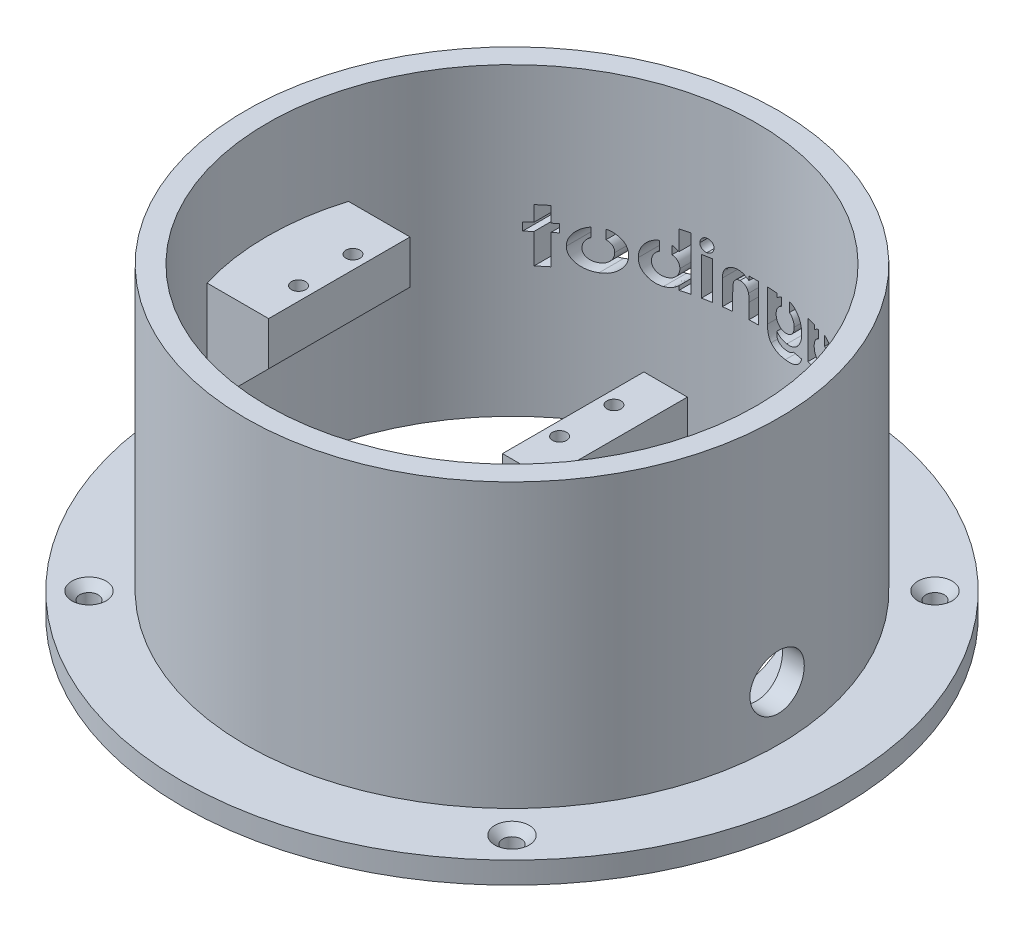
SolidWorks part; units mm, degrees
ref_plane "Front Plane" through (0, 0, 0) normal (0, 0, 1) x (1, 0, 0)
ref_plane "Top Plane" through (0, 0, 0) normal (0, 1, 0) x (1, 0, 0)
ref_plane "Right Plane" through (0, 0, 0) normal (1, 0, 0) x (0, 0, -1)
sketch "Sketch1" plane through (0, 0, 0) normal (0, 1, 0) x (1, 0, 0)
  circle A0 centre (0, 0) radius 60.625
  circle A1 centre (0, 0) radius 45
  dimension "D1" = 121.25
  dimension "D2" = 90
extrude "Boss-Extrude1" add sketch "Sketch1" along normal blind 4 contours A0
sketch "Sketch2" plane through (0, 4, 0) normal (0, 1, 0) x (1, 0, 0)
  circle A0 centre (0, 0) radius 45 construction
  circle A1 centre (0, 0) radius 45
  circle A2 centre (0, 0) radius 49
  dimension "D1" = 4
extrude "Boss-Extrude2" add sketch "Sketch2" along normal blind 52
ref_plane "Plane1" through (0, 36, 0) normal (0, 1, 0) x (1, 0, 0)
sketch "Sketch4" plane through (0, 0, 0) normal (0, 0, 1) x (1, 0, 0)
  line L0 (-60.625, 0) -> (60.625, 0) construction
  line L1 (11.25, 38) -> (19.25, 38)
  line L2 (11.25, 38) -> (11.25, 0)
  line L3 (11.25, 0) -> (19.25, 0)
  line L4 (19.25, 38) -> (19.25, 0)
  line L5 (49, 56) -> (-49, 56) construction
  line L6 (-45, 56) -> (-45, 4)
  line L7 (-31.75, 38) -> (-46.75, 38)
  line L8 (-31.75, 38) -> (-31.75, 30)
  line L9 (-31.75, 30) -> (-46.75, 30)
  line L10 (-46.75, 38) -> (-46.75, 30)
  line L11 (60.625, 4) -> (-60.625, 4) construction
  line L12 (-31.75, 30) -> (-45, 16.75)
  dimension "D1" = 11.25
  dimension "D2" = 8
  dimension "D3" = 18
  dimension "D4" = 43
  dimension "D5" = 15
  dimension "D6" = 8
  dimension "D7" = 45
  dimension "D8" = 18
extrude "Boss-Extrude4" add sketch "Sketch4" along normal mid plane 26 contours L9 L8 L7 L6 | L12 L9 L6 | L1 L4 L3 L2
sketch "Sketch5" plane through (0, 0, 0) normal (0, -1, 0) x (1, 0, 0)
  line L0 (11.25, 13) -> (29.0674, 34.3524)
  line L1 (11.25, -13) -> (29.0674, -34.3524)
  line L2 (11.25, 13) -> (11.25, -13)
  circle A0 centre (0, 0) radius 45 construction
  arc A1 (29.0674, -34.3524) -> (29.0674, 34.3524) centre (0, 0) ccw
extrude "Boss-Extrude5" add sketch "Sketch5" against normal up to surface (4 mm away) contours L0 A1 L1 L2 up to face at (0, 4, 60.625)
sketch "Sketch7" plane through (0, 38, 0) normal (0, 1, 0) x (1, 0, 0)
  line L0 (-31.75, -13) -> (-31.75, 13) construction
  circle A0 centre (-34.25, 5) radius 1.3
  circle A1 centre (-34.25, -5) radius 1.3
  circle A2 centre (13.75, 5) radius 1.3
  circle A3 centre (13.75, -5) radius 1.3
  dimension "D1" = 2.6
  dimension "D2" = 2.6
  dimension "D3" = 10
  dimension "D4" = 5
  dimension "D5" = 2.5
  dimension "D7" = 48
  dimension "D6" = 2
extrude "Cut-Extrude4" cut sketch "Sketch7" against normal blind 7.2
sketch "Sketch9" plane through (11.25, 0, 0) normal (-1, 0, 0) x (0, 0, 1)
  line L0 (13, 0) -> (-13, 0) construction
  line L1 (-5, 29) -> (5, 29)
  line L2 (-5, 29) -> (-5, 0)
  line L3 (-5, 0) -> (5, 0)
  line L4 (5, 29) -> (5, 0)
  line L5 (-5, 29) -> (5, 0) construction
  line L6 (-5, 0) -> (5, 29) construction
  line L7 (0, 0) -> (0, 29) construction
  line L8 (13, 38) -> (-13, 38) construction
  line L10 (5, 5) -> (-5, 5)
  point P0 (0, 14.5)
  dimension "D1" = 10
  dimension "D2" = 9
  dimension "D3" = 5
extrude "Cut-Extrude7" cut sketch "Sketch9" against normal up to surface (8 mm away) contours L10 L4 L1 L2 up to face at (19.25, 21, 0)
ref_plane "Plane2" through (49, 0, 0) normal (1, 0, 0) x (0, 0, -1)
sketch "Sketch11" plane through (49, 0, 0) normal (1, 0, 0) x (0, 0, -1)
  circle A0 centre (0, 14) radius 5
  dimension "D1" = 10
  dimension "D2" = 14
extrude "Cut-Extrude8" cut sketch "Sketch11" against normal up to next
sketch "Sketch12" plane through (0, 4, 0) normal (0, 1, 0) x (1, 0, 0)
  line L5 (27.25, 19.6878) -> (27.25, -19.6878)
  line L6 (27.25, 19.6878) -> (27.25, -19.6878)
  line L9 (24.25, 16.0926) -> (24.25, -16.0926)
  line L10 (19.25, -13) -> (19.25, 13) construction
  line L18 (27.25, -19.6878) -> (29.4795, -22.3597)
  line L19 (29.4795, 22.3597) -> (27.25, 19.6878)
  line L21 (24.25, -16.0926) -> (29.4795, -22.3597)
  line L22 (29.4795, 22.3597) -> (24.25, 16.0926)
  arc A2 (29.4795, -22.3597) -> (29.4795, 22.3597) centre (0, 0) ccw
  arc A3 (29.4795, -22.3597) -> (29.4795, 22.3597) centre (0, 0) ccw
  dimension "D2" = 5
  dimension "D1" = 8
extrude "Cut-Extrude9" cut sketch "Sketch12" against normal through all contours L21 A3 L22 L6 | L6 L22 L9 L21
sketch "Sketch14" plane through (0, 4, 0) normal (0, 1, 0) x (1, 0, 0)
  line L0 (0, 0) -> (-38.8909, 38.8909) construction
  line L1 (11.25, 13) -> (19.25, 13) construction
  circle A0 centre (-38.8909, 38.8909) radius 1.5
  circle A1 centre (38.8909, 38.8909) radius 1.5
  circle A2 centre (38.8909, -38.8909) radius 1.5
  circle A3 centre (-38.8909, -38.8909) radius 1.5
  point P15 (0, 0)
  dimension "D1" = 3
  dimension "D2" = 55
  dimension "D3" = 135
  dimension "D4" = 4
hole_wizard "CSK for M3 Countersunk Flat Head Screw1" positions "Sketch15" profile "Sketch17" countersink size "M3" standard "DIN" end condition up to next
sketch "Sketch15" plane through (0, 4, 0) normal (0, 1, 0) x (1, 0, 0)
  point P0 (-38.8909, 38.8909)
  point P3 (-38.8909, -38.8909)
  point P6 (38.8909, -38.8909)
  point P9 (38.8909, 38.8909)
sketch "Sketch17" plane through (-38.8909, 4, -38.8909) normal (1, 0, 0) x (0, 0, 1)
  line L0 (0, 0) -> (0, 4)
  line L1 (0, 4) -> (1.7, 4)
  line L2 (1.7, 4) -> (1.7, 1.45)
  line L3 (1.7, 1.45) -> (3.15, 0)
  line L5 (3.15, 0) -> (0, 0)
  line L6 (-1.7, 1.45) -> (-3.15, 0) construction
  line L11 (0, -6.35) -> (0, 107.95) construction
  dimension "Thru Hole Dia." = 3.4
  dimension "Thru Hole Depth" = 4
  dimension "Near C'Sink Dia." = 6.3
  dimension "Near C'Sink Angle" = 90
sketch "Sketch18" plane through (0, 0, -13) normal (0, 0, -1) x (-1, 0, 0)
  line L1 (28.0255, 33.7692) -> (29.7351, 33.7692)
  line L2 (29.7351, 33.7692) -> (29.7351, 30.9606)
  line L3 (29.7351, 30.9606) -> (30.8341, 30.9606)
  line L4 (30.8341, 30.9606) -> (30.8341, 29.4952)
  line L5 (30.8341, 29.4952) -> (29.7351, 29.4952)
  line L6 (29.7351, 29.4952) -> (29.7351, 24)
  line L7 (29.7351, 24) -> (28.0255, 24)
  line L8 (28.0255, 24) -> (28.0255, 29.4952)
  line L9 (28.0255, 29.4952) -> (27.1707, 29.4952)
  line L10 (27.1707, 29.4952) -> (27.1707, 30.9606)
  line L11 (27.1707, 30.9606) -> (28.0255, 30.9606)
  line L12 (28.0255, 30.9606) -> (28.0255, 33.7692)
  line L13 (12.5168, 33.7692) -> (12.5168, 30.1497)
  line L14 (12.5168, 24.7594) -> (12.5168, 24)
  line L15 (12.5168, 24) -> (10.8072, 24)
  line L16 (10.8072, 24) -> (10.8072, 33.7692)
  line L17 (10.8072, 33.7692) -> (12.5168, 33.7692)
  line L18 (7.5101, 30.9606) -> (9.2197, 30.9606)
  line L19 (9.2197, 30.9606) -> (9.2197, 24)
  line L20 (9.2197, 24) -> (7.5101, 24)
  line L21 (7.5101, 24) -> (7.5101, 30.9606)
  line L22 (-0.3053, 30.9606) -> (1.4043, 30.9606)
  line L23 (1.4043, 30.9606) -> (1.4043, 30.2241)
  line L24 (5.9226, 28.5641) -> (5.9226, 24)
  line L25 (5.9226, 24) -> (4.213, 24)
  line L26 (4.213, 24) -> (4.213, 27.0224)
  line L27 (1.4043, 26.7705) -> (1.4043, 24)
  line L28 (1.4043, 24) -> (-0.3053, 24)
  line L29 (-0.3053, 24) -> (-0.3053, 30.9606)
  line L30 (-3.8466, 30.9606) -> (-2.0149, 30.9606)
  line L31 (-2.0149, 30.9606) -> (-2.0149, 25.0227)
  line L32 (-9.2273, 23.5115) -> (-7.3269, 23.5115)
  line L33 (-3.8466, 30.1859) -> (-3.8466, 30.9606)
  line L34 (-12.3947, 30.9606) -> (-10.6851, 30.9606)
  line L35 (-10.6851, 30.9606) -> (-10.6851, 24)
  line L36 (-10.6851, 24) -> (-12.3947, 24)
  line L37 (-12.3947, 24) -> (-12.3947, 24.7594)
  line L38 (-12.3947, 30.1764) -> (-12.3947, 30.9606)
  line L39 (-30.1014, 30.9606) -> (-28.3918, 30.9606)
  line L40 (-28.3918, 30.9606) -> (-28.3918, 30.1287)
  line L41 (-19.3553, 28.0489) -> (-19.3553, 24)
  line L42 (-19.3553, 24) -> (-21.0649, 24)
  line L43 (-21.0649, 24) -> (-21.0649, 27.4956)
  line L44 (-23.8736, 27.1082) -> (-23.8736, 24)
  line L45 (-23.8736, 24) -> (-25.5832, 24)
  line L46 (-25.5832, 24) -> (-25.5832, 27.3372)
  line L47 (-28.3918, 27.0643) -> (-28.3918, 24)
  line L48 (-28.3918, 24) -> (-30.1014, 24)
  line L49 (-30.1014, 24) -> (-30.1014, 30.9606)
  line L51 (-15.1048, 31.4629) -> (-13.3948, 31.4629)
  line L52 (-15.1048, 31.4629) -> (-15.1048, 28.9712)
  line L53 (-15.1048, 28.9712) -> (-13.3948, 28.9712)
  line L54 (-13.3948, 31.4629) -> (-13.3948, 28.9712)
  line L55 (-6.4773, 31.5143) -> (-4.7673, 31.5143)
  line L56 (-6.4773, 31.5143) -> (-6.4773, 29.0876)
  line L57 (-6.4773, 29.0876) -> (-4.7673, 29.0876)
  line L58 (-4.7673, 31.5143) -> (-4.7673, 29.0876)
  line L59 (13.5081, 31.593) -> (15.2181, 31.593)
  line L60 (13.5081, 31.593) -> (13.5081, 28.9616)
  line L61 (13.5081, 28.9616) -> (15.2181, 28.9616)
  line L62 (15.2181, 31.593) -> (15.2181, 28.9616)
  line L63 (21.9818, 31.4887) -> (23.6918, 31.4887)
  line L64 (21.9818, 31.4887) -> (21.9818, 28.7761)
  line L65 (21.9818, 28.7761) -> (23.6918, 28.7761)
  line L66 (23.6918, 31.4887) -> (23.6918, 28.7761)
  spline S0 degree 3 poles (22.7936, 31.0827) (22.9536, 31.0827) (23.1931, 31.0681) (23.5072, 31.016) (23.7386, 30.9659) (23.965, 30.8957) (24.1877, 30.8115) (24.4086, 30.7149) (24.6222, 30.5998) (24.83, 30.4751) (25.0271, 30.3374) (25.2118, 30.188) (25.3874, 30.0303) (25.5458, 29.8573) (25.6972, 29.6776) (25.8334, 29.4845) (25.9594, 29.2828) (26.0716, 29.0738) (26.169, 28.8587) (26.2536, 28.6407) (26.3198, 28.417) (26.3746, 28.1906) (26.4213, 27.88) (26.4389, 27.6443) (26.438, 27.486) knots 0 0 0 0 0.084364 0.126142 0.167706 0.209066 0.250973 0.293148 0.336041 0.378761 0.420893 0.462622 0.503914 0.545188 0.586138 0.627722 0.669585 0.711432 0.752691 0.793971 0.834592 0.875577 0.91664 1 1 1 1
  spline S1 degree 3 poles (26.438, 27.486) (26.4378, 27.3266) (26.4236, 27.0883) (26.3713, 26.7763) (26.321, 26.5461) (26.2511, 26.3218) (26.1694, 26.1) (26.0691, 25.8836) (25.9582, 25.6704) (25.8314, 25.4666) (25.6953, 25.2716) (25.5446, 25.0905) (25.3874, 24.9177) (25.2164, 24.759) (25.0341, 24.6119) (24.8423, 24.4746) (24.6396, 24.3502) (24.4285, 24.2409) (24.2126, 24.1424) (23.9906, 24.0604) (23.763, 23.9934) (23.5297, 23.9417) (23.2093, 23.8941) (22.9652, 23.8771) (22.8012, 23.8779) knots 0 0 0 0 0.083839 0.125192 0.166335 0.207602 0.24867 0.290582 0.332926 0.374978 0.416741 0.457857 0.498809 0.539516 0.58042 0.62191 0.663502 0.705394 0.746864 0.788245 0.829736 0.871532 0.913825 1 1 1 1
  spline S2 degree 3 poles (22.8012, 23.8779) (22.5631, 23.8803) (22.2083, 23.9072) (21.7532, 24.019) (21.429, 24.1339) (21.1177, 24.2814) (20.822, 24.4638) (20.5389, 24.6777) (20.2733, 24.9212) (20.03, 25.1884) (19.8174, 25.4736) (19.6369, 25.7726) (19.4887, 26.0857) (19.3743, 26.4132) (19.2623, 26.874) (19.2355, 27.2332) (19.2332, 27.4746) knots 0 0 0 0 0.126884 0.188201 0.248894 0.309599 0.371125 0.433466 0.498143 0.562593 0.625474 0.687114 0.748125 0.809457 0.871431 1 1 1 1
  spline S3 degree 3 poles (19.2332, 27.4746) (19.2336, 27.7324) (19.2684, 28.1141) (19.3922, 28.6033) (19.5227, 28.9481) (19.6897, 29.2762) (19.9647, 29.6971) (20.2255, 29.9763) (20.4143, 30.1497) knots 0 0 0 0 0.256474 0.379237 0.500978 0.622367 0.744855 1 1 1 1
  spline S4 degree 3 poles (20.4143, 30.1497) (20.5802, 30.3024) (20.8481, 30.5037) (21.2311, 30.7219) (21.5244, 30.8552) (21.8286, 30.9555) (22.2495, 31.0542) (22.575, 31.0818) (22.7936, 31.0827) knots 0 0 0 0 0.258464 0.38258 0.504991 0.627227 0.749297 1 1 1 1
  spline S5 degree 3 poles (22.8318, 29.4952) (22.7019, 29.4917) (22.5077, 29.4823) (22.2621, 29.4178) (22.0874, 29.3572) (21.9227, 29.2762) (21.7633, 29.1814) (21.6176, 29.0627) (21.4785, 28.9326) (21.3522, 28.7881) (21.2446, 28.6306) (21.1485, 28.4663) (21.0755, 28.289) (21.0153, 28.1036) (20.9595, 27.8373) (20.9404, 27.6306) (20.9428, 27.4898) knots 0 0 0 0 0.126803 0.187423 0.246518 0.306285 0.365703 0.426477 0.488622 0.550895 0.612679 0.673914 0.735734 0.798735 0.86329 1 1 1 1
  spline S6 degree 3 poles (20.9428, 27.4898) (20.9422, 27.3456) (20.9565, 27.1333) (21.0136, 26.8609) (21.0729, 26.672) (21.1476, 26.4928) (21.2392, 26.3242) (21.3487, 26.1674) (21.4728, 26.0226) (21.6088, 25.891) (21.7577, 25.7782) (21.9134, 25.6801) (22.0795, 25.6014) (22.2535, 25.5406) (22.5012, 25.4797) (22.6954, 25.468) (22.826, 25.4654) knots 0 0 0 0 0.139456 0.204809 0.268587 0.330587 0.392213 0.45361 0.515092 0.576402 0.636039 0.695407 0.753981 0.813285 0.873377 1 1 1 1
  spline S7 degree 3 poles (22.826, 25.4654) (22.9571, 25.4658) (23.1512, 25.4829) (23.3999, 25.5421) (23.5754, 25.6033) (23.7416, 25.6838) (23.899, 25.7823) (24.0491, 25.8968) (24.1868, 26.0308) (24.3144, 26.1761) (24.4262, 26.3337) (24.5196, 26.5022) (24.5963, 26.6806) (24.6557, 26.8685) (24.7119, 27.1379) (24.7308, 27.3472) (24.7284, 27.4898) knots 0 0 0 0 0.126397 0.186939 0.246099 0.305348 0.364572 0.424924 0.486952 0.54955 0.611149 0.672922 0.73501 0.798049 0.862643 1 1 1 1
  spline S8 degree 3 poles (24.7284, 27.4898) (24.7289, 27.6322) (24.7144, 27.8419) (24.6579, 28.1106) (24.5978, 28.2968) (24.5236, 28.4736) (24.4319, 28.6402) (24.3219, 28.7958) (24.1971, 28.9395) (24.0592, 29.0692) (23.9128, 29.1849) (23.7547, 29.2805) (23.5879, 29.3593) (23.4118, 29.42) (23.161, 29.4811) (22.9643, 29.4923) (22.8318, 29.4952) knots 0 0 0 0 0.13784 0.202698 0.265406 0.326938 0.388125 0.449117 0.511101 0.572086 0.632197 0.691339 0.750564 0.810546 0.871335 1 1 1 1
  spline S9 degree 3 poles (12.5168, 30.1497) (12.6689, 30.2999) (12.913, 30.5045) (13.2701, 30.721) (13.5425, 30.8554) (13.8263, 30.9547) (14.2179, 31.0586) (14.5242, 31.079) (14.7283, 31.0827) knots 0 0 0 0 0.260396 0.385476 0.507708 0.62942 0.750914 1 1 1 1
  spline S10 degree 3 poles (14.7283, 31.0827) (14.9489, 31.0835) (15.2774, 31.0537) (15.6975, 30.9454) (15.9965, 30.8341) (16.2816, 30.6893) (16.5559, 30.5161) (16.8147, 30.3071) (17.0582, 30.0704) (17.2834, 29.811) (17.4794, 29.5289) (17.6425, 29.228) (17.7809, 28.9116) (17.8817, 28.5747) (17.9877, 28.0953) (18.0097, 27.72) (18.012, 27.4669) knots 0 0 0 0 0.12138 0.180256 0.238142 0.296489 0.355776 0.416247 0.479076 0.54232 0.604902 0.667516 0.730346 0.794405 0.860608 1 1 1 1
  spline S11 degree 3 poles (18.012, 27.4669) (18.0112, 27.2212) (17.9853, 26.8569) (17.8789, 26.39) (17.7693, 26.061) (17.6298, 25.7471) (17.4595, 25.4483) (17.2574, 25.1658) (17.0264, 24.9033) (16.774, 24.6656) (16.511, 24.4523) (16.2322, 24.2776) (15.9446, 24.1299) (15.6435, 24.0172) (15.2231, 23.91) (14.8966, 23.875) (14.6767, 23.8779) knots 0 0 0 0 0.135343 0.199959 0.263049 0.325881 0.388744 0.451973 0.516706 0.580831 0.6426 0.702706 0.761562 0.820266 0.879182 1 1 1 1
  spline S12 degree 3 poles (14.6767, 23.8779) (14.4813, 23.879) (14.1903, 23.9014) (13.8164, 23.9898) (13.5471, 24.0796) (13.2849, 24.2024) (12.9279, 24.4129) (12.6786, 24.6134) (12.5168, 24.7594) knots 0 0 0 0 0.245253 0.364043 0.481077 0.600625 0.726476 1 1 1 1
  spline S13 degree 3 poles (14.3581, 29.4952) (14.2224, 29.4925) (14.0206, 29.4811) (13.7637, 29.4198) (13.5821, 29.3613) (13.4104, 29.2824) (13.2472, 29.1868) (13.0939, 29.0727) (12.9496, 28.9448) (12.82, 28.8008) (12.7049, 28.647) (12.6094, 28.4813) (12.5298, 28.3059) (12.4697, 28.1188) (12.409, 27.8506) (12.3972, 27.6408) (12.3947, 27.4994) knots 0 0 0 0 0.129944 0.191681 0.251804 0.311878 0.37178 0.43216 0.494106 0.5556 0.61683 0.677256 0.737884 0.800505 0.864611 1 1 1 1
  spline S14 degree 3 poles (12.3947, 27.4994) (12.3973, 27.3547) (12.409, 27.1406) (12.4693, 26.8672) (12.5306, 26.6767) (12.6089, 26.497) (12.7043, 26.3272) (12.8207, 26.1712) (12.9489, 26.0235) (13.094, 25.8938) (13.2466, 25.7775) (13.4104, 25.6817) (13.5829, 25.6041) (13.7629, 25.5396) (14.0209, 25.4803) (14.2222, 25.4676) (14.3581, 25.4654) knots 0 0 0 0 0.137034 0.201676 0.264245 0.325918 0.386785 0.447889 0.509667 0.571399 0.631536 0.690841 0.750317 0.810229 0.871351 1 1 1 1
  spline S15 degree 3 poles (14.3581, 25.4654) (14.4904, 25.4663) (14.6858, 25.4825) (14.9372, 25.5423) (15.1143, 25.6051) (15.2837, 25.6869) (15.4466, 25.7826) (15.5976, 25.9021) (15.7426, 26.0336) (15.8723, 26.1818) (15.9886, 26.3392) (16.0864, 26.5074) (16.164, 26.6867) (16.2281, 26.8738) (16.2876, 27.1426) (16.2999, 27.3521) (16.3024, 27.4936) knots 0 0 0 0 0.1264 0.186368 0.246314 0.305548 0.365765 0.426397 0.489164 0.552425 0.614149 0.675935 0.737677 0.800494 0.864605 1 1 1 1
  spline S16 degree 3 poles (16.3024, 27.4936) (16.2994, 27.6337) (16.2886, 27.8419) (16.2268, 28.1069) (16.1694, 28.2934) (16.0892, 28.4684) (15.9943, 28.634) (15.8827, 28.7908) (15.7531, 28.9344) (15.6111, 29.0651) (15.4595, 29.1807) (15.2988, 29.2792) (15.127, 29.3568) (14.9481, 29.4206) (14.6922, 29.4804) (14.4927, 29.4929) (14.3581, 29.4952) knots 0 0 0 0 0.134802 0.198611 0.260756 0.321667 0.382903 0.4437 0.505935 0.568128 0.628667 0.688638 0.748437 0.809234 0.870665 1 1 1 1
  spline S17 degree 3 poles (8.3611, 33.8913) (8.5057, 33.8937) (8.7226, 33.8489) (8.977, 33.7027) (9.1452, 33.5539) (9.285, 33.3759) (9.4295, 33.1075) (9.4611, 32.8768) (9.4639, 32.7255) knots 0 0 0 0 0.242963 0.363855 0.490606 0.61874 0.7433 1 1 1 1
  spline S18 degree 3 poles (9.4639, 32.7255) (9.4628, 32.5754) (9.4267, 32.3489) (9.2879, 32.0806) (9.147, 31.9053) (8.9806, 31.7588) (8.732, 31.6103) (8.5162, 31.5712) (8.3744, 31.5712) knots 0 0 0 0 0.256469 0.381955 0.510704 0.637377 0.757775 1 1 1 1
  spline S19 degree 3 poles (8.3744, 31.5712) (8.2284, 31.5686) (8.0103, 31.614) (7.7524, 31.7591) (7.5849, 31.9109) (7.4436, 32.0902) (7.3049, 32.3653) (7.2655, 32.5959) (7.2659, 32.7503) knots 0 0 0 0 0.242759 0.363443 0.489711 0.617482 0.74228 1 1 1 1
  spline S20 degree 3 poles (7.2659, 32.7503) (7.2683, 32.8988) (7.3018, 33.124) (7.4428, 33.3874) (7.5816, 33.5622) (7.7483, 33.7082) (8.0025, 33.8499) (8.2174, 33.8925) (8.3611, 33.8913) knots 0 0 0 0 0.255027 0.378937 0.506523 0.634371 0.754976 1 1 1 1
  spline S21 degree 3 poles (1.4043, 30.2241) (1.5881, 30.3723) (1.8638, 30.5692) (2.2391, 30.781) (2.4966, 30.8962) (2.749, 30.9789) (3.0835, 31.0586) (3.3399, 31.0837) (3.5108, 31.0827) knots 0 0 0 0 0.304989 0.436681 0.556242 0.668759 0.779379 1 1 1 1
  spline S22 degree 3 poles (3.5108, 31.0827) (3.6804, 31.0808) (3.9334, 31.0645) (4.2568, 30.9851) (4.4874, 30.9076) (4.7072, 30.8051) (4.9922, 30.6415) (5.182, 30.4798) (5.3025, 30.3653) knots 0 0 0 0 0.257369 0.381171 0.503299 0.625248 0.747811 1 1 1 1
  spline S23 degree 3 poles (5.3025, 30.3653) (5.4059, 30.2627) (5.5432, 30.0886) (5.6853, 29.8262) (5.7737, 29.6095) (5.8389, 29.3729) (5.908, 29.0248) (5.9215, 28.7507) (5.9226, 28.5641) knots 0 0 0 0 0.22321 0.337546 0.456528 0.581244 0.713405 1 1 1 1
  spline S24 degree 3 poles (4.213, 27.0224) (4.2125, 27.2112) (4.2108, 27.4817) (4.1962, 27.8244) (4.1868, 28.0428) (4.1682, 28.2348) (4.1514, 28.4014) (4.1257, 28.5411) (4.0922, 28.6915) (4.0338, 28.8525) (3.943, 29.0221) (3.8279, 29.1662) (3.6932, 29.2858) (3.5389, 29.3803) (3.303, 29.4721) (3.1097, 29.4957) (2.9785, 29.4952) knots 0 0 0 0 0.179518 0.256937 0.32593 0.387213 0.440139 0.484952 0.522188 0.586422 0.647004 0.704202 0.760716 0.817414 0.875213 1 1 1 1
  spline S25 degree 3 poles (2.9785, 29.4952) (2.8055, 29.4934) (2.5449, 29.4553) (2.234, 29.3024) (2.0255, 29.1462) (1.8416, 28.9531) (1.6327, 28.637) (1.531, 28.3636) (1.4845, 28.171) knots 0 0 0 0 0.240658 0.35739 0.477137 0.600009 0.725225 1 1 1 1
  spline S26 degree 3 poles (1.4845, 28.171) (1.4665, 28.1021) (1.4533, 27.9851) (1.4322, 27.8146) (1.4255, 27.6513) (1.4141, 27.4645) (1.4081, 27.168) (1.4044, 26.934) (1.4043, 26.7705) knots 0 0 0 0 0.151476 0.251213 0.366854 0.500124 0.650932 1 1 1 1
  spline S27 degree 3 poles (-2.0149, 25.0227) (-2.0161, 24.7489) (-2.0329, 24.3502) (-2.1079, 23.8416) (-2.1856, 23.5018) (-2.2863, 23.192) (-2.4455, 22.8255) (-2.6034, 22.5793) (-2.7266, 22.4354) knots 0 0 0 0 0.300234 0.436257 0.562885 0.681681 0.792784 1 1 1 1
  spline S28 degree 3 poles (-2.7266, 22.4354) (-2.8834, 22.2492) (-3.1574, 22.0013) (-3.5792, 21.7441) (-3.9268, 21.5849) (-4.3051, 21.4638) (-4.8649, 21.3434) (-5.3059, 21.3128) (-5.6078, 21.3135) knots 0 0 0 0 0.228421 0.343997 0.462956 0.586703 0.716303 1 1 1 1
  spline S29 degree 3 poles (-5.6078, 21.3135) (-5.9233, 21.3133) (-6.3802, 21.3376) (-6.9551, 21.4475) (-7.33, 21.5582) (-7.6699, 21.7012) (-7.9812, 21.8726) (-8.2633, 22.0776) (-8.5206, 22.3079) (-8.7467, 22.5689) (-9.0083, 22.9588) (-9.1528, 23.2846) (-9.2273, 23.5115) knots 0 0 0 0 0.207411 0.299345 0.383942 0.46371 0.541137 0.616855 0.692287 0.767513 0.843065 1 1 1 1
  spline S30 degree 3 poles (-7.3269, 23.5115) (-7.2424, 23.411) (-7.0944, 23.2762) (-6.8653, 23.1368) (-6.6744, 23.0501) (-6.4646, 22.9844) (-6.1522, 22.9154) (-5.9045, 22.902) (-5.7356, 22.901) knots 0 0 0 0 0.223655 0.337943 0.455777 0.579824 0.711809 1 1 1 1
  spline S31 degree 3 poles (-5.7356, 22.901) (-5.5252, 22.8993) (-5.2245, 22.9236) (-4.8512, 23.0143) (-4.621, 23.1109) (-4.4224, 23.227) (-4.2567, 23.3619) (-4.1198, 23.5105) (-4.0303, 23.6502) (-3.9771, 23.777) (-3.9409, 23.8865) (-3.9134, 24.0127) (-3.8884, 24.1533) (-3.8697, 24.31) (-3.8523, 24.5498) (-3.8442, 24.7376) (-3.8466, 24.8682) knots 0 0 0 0 0.197721 0.282266 0.359994 0.431569 0.49787 0.56009 0.620807 0.652682 0.689174 0.72906 0.773983 0.823375 0.87735 1 1 1 1
  spline S32 degree 3 poles (-3.8466, 24.8682) (-3.9891, 24.7215) (-4.2155, 24.5237) (-4.5479, 24.3175) (-4.7977, 24.1973) (-5.0596, 24.1094) (-5.435, 24.0229) (-5.7297, 24.001) (-5.9302, 24) knots 0 0 0 0 0.263928 0.385524 0.503705 0.620733 0.741155 1 1 1 1
  spline S33 degree 3 poles (-5.9302, 24) (-6.1529, 23.9985) (-6.4834, 24.0299) (-6.9074, 24.1357) (-7.2089, 24.2439) (-7.4948, 24.3877) (-7.7693, 24.5588) (-8.0273, 24.7661) (-8.2723, 24.9982) (-8.4938, 25.2561) (-8.6886, 25.5331) (-8.8529, 25.8273) (-8.9865, 26.1384) (-9.0929, 26.4651) (-9.1927, 26.932) (-9.2188, 27.2956) (-9.2197, 27.5413) knots 0 0 0 0 0.1237 0.183445 0.242476 0.301273 0.360988 0.421869 0.484864 0.548268 0.610431 0.67277 0.73514 0.798288 0.86338 1 1 1 1
  spline S34 degree 3 poles (-9.2197, 27.5413) (-9.2211, 27.8026) (-9.1909, 28.1873) (-9.0852, 28.6807) (-8.9753, 29.0233) (-8.8304, 29.3443) (-8.5973, 29.747) (-8.3769, 30.0193) (-8.2104, 30.1821) knots 0 0 0 0 0.269734 0.396745 0.520319 0.640547 0.759724 1 1 1 1
  spline S35 degree 3 poles (-8.2104, 30.1821) (-8.0629, 30.3284) (-7.8246, 30.5246) (-7.4774, 30.7358) (-7.2084, 30.8619) (-6.9288, 30.9621) (-6.5361, 31.0571) (-6.2309, 31.0833) (-6.0256, 31.0827) knots 0 0 0 0 0.256681 0.379784 0.501471 0.623319 0.746312 1 1 1 1
  spline S36 degree 3 poles (-6.0256, 31.0827) (-5.8329, 31.0809) (-5.544, 31.0597) (-5.1722, 30.9687) (-4.9013, 30.8759) (-4.6336, 30.7555) (-4.2695, 30.5388) (-4.0124, 30.3368) (-3.8466, 30.1859) knots 0 0 0 0 0.2398 0.357658 0.474596 0.595177 0.721609 1 1 1 1
  spline S37 degree 3 poles (-5.6173, 29.4952) (-5.7486, 29.4924) (-5.9441, 29.481) (-6.1927, 29.4198) (-6.3686, 29.3613) (-6.5347, 29.2825) (-6.6914, 29.1864) (-6.8405, 29.0749) (-6.9773, 28.9458) (-7.1041, 28.8063) (-7.2105, 28.6527) (-7.3054, 28.4939) (-7.3792, 28.3235) (-7.4401, 28.1459) (-7.4912, 27.8909) (-7.5138, 27.6945) (-7.5101, 27.5604) knots 0 0 0 0 0.130325 0.192491 0.253031 0.313597 0.374077 0.434784 0.49761 0.560052 0.621032 0.682272 0.742887 0.804621 0.867736 1 1 1 1
  spline S38 degree 3 poles (-7.5101, 27.5604) (-7.5126, 27.4216) (-7.4934, 27.218) (-7.4376, 26.9553) (-7.3761, 26.7729) (-7.2989, 26.5991) (-7.2063, 26.4341) (-7.0919, 26.2817) (-6.9648, 26.1386) (-6.8243, 26.0093) (-6.6731, 25.8968) (-6.5142, 25.7996) (-6.3442, 25.7239) (-6.1669, 25.6625) (-5.9146, 25.6021) (-5.7175, 25.5901) (-5.5849, 25.5875) knots 0 0 0 0 0.134675 0.197932 0.260448 0.321294 0.382443 0.443854 0.505984 0.568072 0.628986 0.688849 0.748568 0.809329 0.870916 1 1 1 1
  spline S39 degree 3 poles (-5.5849, 25.5875) (-5.4549, 25.585) (-5.2638, 25.604) (-5.0182, 25.6605) (-4.8459, 25.7195) (-4.6833, 25.7967) (-4.5283, 25.8887) (-4.3842, 26) (-4.2481, 26.1259) (-4.1254, 26.2659) (-4.017, 26.4176) (-3.928, 26.581) (-3.8521, 26.7535) (-3.796, 26.9376) (-3.7378, 27.2011) (-3.7243, 27.4074) (-3.7245, 27.5471) knots 0 0 0 0 0.128347 0.189068 0.248938 0.308024 0.366703 0.426834 0.487805 0.549753 0.610659 0.671749 0.733442 0.796702 0.861717 1 1 1 1
  spline S40 degree 3 poles (-3.7245, 27.5471) (-3.724, 27.6849) (-3.7381, 27.8886) (-3.7959, 28.149) (-3.8527, 28.3315) (-3.9269, 28.5039) (-4.02, 28.6647) (-4.1263, 28.8169) (-4.2516, 28.9552) (-4.3866, 29.0832) (-4.5355, 29.1914) (-4.6907, 29.2871) (-4.8576, 29.3629) (-5.034, 29.4225) (-5.2869, 29.4785) (-5.4835, 29.4978) (-5.6173, 29.4952) knots 0 0 0 0 0.135592 0.199609 0.261895 0.32322 0.383708 0.44425 0.505361 0.566852 0.626748 0.685936 0.745803 0.8065 0.868686 1 1 1 1
  spline S41 degree 3 poles (-12.3947, 24.7594) (-12.5564, 24.6133) (-12.8058, 24.4129) (-13.1627, 24.2024) (-13.4245, 24.08) (-13.6923, 23.9898) (-14.0649, 23.9011) (-14.3554, 23.8792) (-14.5508, 23.8779) knots 0 0 0 0 0.273944 0.399987 0.519719 0.636176 0.754371 1 1 1 1
  spline S42 degree 3 poles (-14.5508, 23.8779) (-14.7712, 23.8755) (-15.0979, 23.9093) (-15.5182, 24.0175) (-15.819, 24.1304) (-16.1079, 24.2769) (-16.3871, 24.453) (-16.6518, 24.6649) (-16.9042, 24.9034) (-17.1353, 25.1657) (-17.3374, 25.4483) (-17.5076, 25.7471) (-17.6472, 26.061) (-17.7568, 26.39) (-17.8632, 26.8569) (-17.8891, 27.2212) (-17.8899, 27.4669) knots 0 0 0 0 0.121092 0.179634 0.238304 0.297437 0.357507 0.419513 0.4836 0.548295 0.611487 0.674313 0.737107 0.80016 0.864737 1 1 1 1
  spline S43 degree 3 poles (-17.8899, 27.4669) (-17.8879, 27.7201) (-17.865, 28.0952) (-17.7604, 28.5752) (-17.6558, 28.9108) (-17.5211, 29.2285) (-17.357, 29.5288) (-17.1614, 29.811) (-16.936, 30.0703) (-16.6926, 30.3079) (-16.4322, 30.5148) (-16.1589, 30.6905) (-15.8723, 30.834) (-15.5726, 30.9447) (-15.1523, 31.0546) (-14.8235, 31.0829) (-14.6023, 31.0827) knots 0 0 0 0 0.139309 0.205474 0.269598 0.332253 0.39483 0.457376 0.520582 0.583374 0.644082 0.70304 0.761664 0.819844 0.878346 1 1 1 1
  spline S44 degree 3 poles (-14.6023, 31.0827) (-14.3968, 31.0851) (-14.092, 31.0547) (-13.6981, 30.9597) (-13.4159, 30.86) (-13.1421, 30.7337) (-12.7892, 30.5205) (-12.5451, 30.3239) (-12.3947, 30.1764) knots 0 0 0 0 0.251537 0.373434 0.495667 0.61768 0.742091 1 1 1 1
  spline S45 degree 3 poles (-14.2436, 29.4952) (-14.377, 29.4931) (-14.5751, 29.4799) (-14.8293, 29.4209) (-15.0069, 29.3568) (-15.1771, 29.2787) (-15.3374, 29.1808) (-15.489, 29.0651) (-15.631, 28.9344) (-15.7605, 28.7908) (-15.8722, 28.634) (-15.9671, 28.4684) (-16.0473, 28.2934) (-16.1047, 28.1069) (-16.1665, 27.8419) (-16.1773, 27.6337) (-16.1803, 27.4936) knots 0 0 0 0 0.128421 0.189996 0.250359 0.309744 0.369856 0.430537 0.492876 0.555257 0.616197 0.677577 0.738631 0.800922 0.864882 1 1 1 1
  spline S46 degree 3 poles (-16.1803, 27.4936) (-16.1778, 27.3521) (-16.1656, 27.1426) (-16.106, 26.8738) (-16.042, 26.6866) (-15.9639, 26.5079) (-15.8688, 26.3387) (-15.752, 26.1818) (-15.6223, 26.0337) (-15.4774, 25.9014) (-15.3249, 25.7839) (-15.1629, 25.6856) (-14.993, 25.6061) (-14.8159, 25.5415) (-14.5641, 25.4833) (-14.3684, 25.466) (-14.236, 25.4654) knots 0 0 0 0 0.135365 0.199461 0.262264 0.323991 0.385461 0.447171 0.510418 0.573171 0.634271 0.693954 0.753723 0.813084 0.873629 1 1 1 1
  spline S47 degree 3 poles (-14.236, 25.4654) (-14.1001, 25.4676) (-13.8988, 25.4803) (-13.6408, 25.5396) (-13.4608, 25.6041) (-13.2882, 25.6817) (-13.1246, 25.7776) (-12.9718, 25.8931) (-12.8289, 26.0249) (-12.698, 26.1697) (-12.5848, 26.3286) (-12.4862, 26.4963) (-12.4087, 26.6768) (-12.3471, 26.8671) (-12.2869, 27.1406) (-12.2752, 27.3547) (-12.2726, 27.4994) knots 0 0 0 0 0.128662 0.18979 0.249707 0.309189 0.3685 0.428644 0.489937 0.552121 0.612878 0.67405 0.735729 0.798305 0.862953 1 1 1 1
  spline S48 degree 3 poles (-12.2726, 27.4994) (-12.2751, 27.6409) (-12.2869, 27.8506) (-12.3476, 28.1188) (-12.4078, 28.3058) (-12.4868, 28.482) (-12.5854, 28.6457) (-12.6974, 28.8023) (-12.8297, 28.9432) (-12.9718, 29.0741) (-13.1269, 29.1861) (-13.2901, 29.2825) (-13.4624, 29.3617) (-13.6455, 29.4197) (-13.9043, 29.4809) (-14.1072, 29.4927) (-14.2436, 29.4952) knots 0 0 0 0 0.135096 0.199063 0.261548 0.322044 0.382646 0.443385 0.505155 0.566516 0.627254 0.687026 0.74697 0.807539 0.869733 1 1 1 1
  spline S49 degree 3 poles (-28.3918, 30.1287) (-28.2465, 30.2839) (-28.0093, 30.4927) (-27.6591, 30.7169) (-27.3865, 30.8514) (-27.1007, 30.954) (-26.6986, 31.0562) (-26.3842, 31.0813) (-26.1728, 31.0827) knots 0 0 0 0 0.256336 0.379114 0.500551 0.622116 0.744715 1 1 1 1
  spline S50 degree 3 poles (-26.1728, 31.0827) (-25.9608, 31.0835) (-25.6457, 31.0468) (-25.2501, 30.9122) (-24.9764, 30.771) (-24.7204, 30.5963) (-24.4112, 30.3022) (-24.2256, 30.0355) (-24.1235, 29.8425) knots 0 0 0 0 0.251955 0.373414 0.494801 0.617069 0.74062 1 1 1 1
  spline S51 degree 3 poles (-24.1235, 29.8425) (-23.9889, 30.0382) (-23.7549, 30.3055) (-23.3883, 30.5963) (-23.0919, 30.7723) (-22.7775, 30.9117) (-22.333, 31.046) (-21.9839, 31.0836) (-21.7499, 31.0827) knots 0 0 0 0 0.255445 0.379177 0.501905 0.625344 0.748278 1 1 1 1
  spline S52 degree 3 poles (-21.7499, 31.0827) (-21.5115, 31.0848) (-21.1601, 31.0429) (-20.7197, 30.8991) (-20.4251, 30.7465) (-20.1587, 30.5654) (-19.9317, 30.3515) (-19.7433, 30.1122) (-19.6207, 29.8888) (-19.5414, 29.6912) (-19.4935, 29.5193) (-19.4487, 29.3274) (-19.4165, 29.1128) (-19.3865, 28.8776) (-19.3622, 28.5206) (-19.355, 28.2417) (-19.3553, 28.0489) knots 0 0 0 0 0.160904 0.236986 0.311729 0.384307 0.453908 0.521546 0.589232 0.625293 0.665128 0.709632 0.758368 0.811604 0.869763 1 1 1 1
  spline S53 degree 3 poles (-21.0649, 27.4956) (-21.0681, 27.6748) (-21.0704, 27.9329) (-21.1067, 28.2594) (-21.1371, 28.4701) (-21.1807, 28.6571) (-21.2339, 28.8208) (-21.2955, 28.9614) (-21.37, 29.0788) (-21.4534, 29.1777) (-21.5461, 29.2625) (-21.6473, 29.3348) (-21.7578, 29.3965) (-21.8805, 29.4381) (-22.0594, 29.4832) (-22.2008, 29.4974) (-22.2975, 29.4952) knots 0 0 0 0 0.200235 0.287287 0.36626 0.437683 0.50118 0.558021 0.608412 0.655743 0.701944 0.748215 0.794252 0.842505 0.892237 1 1 1 1
  spline S54 degree 3 poles (-22.2975, 29.4952) (-22.4475, 29.4962) (-22.6719, 29.4663) (-22.9494, 29.3564) (-23.1418, 29.2461) (-23.3164, 29.1082) (-23.469, 28.9446) (-23.5951, 28.7544) (-23.6824, 28.5779) (-23.737, 28.4184) (-23.7754, 28.2817) (-23.8054, 28.1272) (-23.8289, 27.9564) (-23.8514, 27.7682) (-23.867, 27.4836) (-23.8766, 27.2617) (-23.8736, 27.1082) knots 0 0 0 0 0.138577 0.206073 0.274463 0.3426 0.41074 0.480118 0.5526 0.591784 0.635663 0.683569 0.736965 0.794871 0.858421 1 1 1 1
  spline S55 degree 3 poles (-25.5832, 27.3372) (-25.5819, 27.4804) (-25.5875, 27.6872) (-25.6029, 27.9524) (-25.6183, 28.128) (-25.6361, 28.288) (-25.6617, 28.4317) (-25.6886, 28.5597) (-25.7348, 28.7052) (-25.7999, 28.8663) (-25.8972, 29.0372) (-26.0148, 29.1803) (-26.1497, 29.2968) (-26.3022, 29.3854) (-26.5292, 29.4757) (-26.7172, 29.4923) (-26.8425, 29.4952) knots 0 0 0 0 0.151067 0.218305 0.280287 0.337064 0.388152 0.434234 0.474994 0.549031 0.617296 0.681663 0.743542 0.80432 0.867013 1 1 1 1
  spline S56 degree 3 poles (-26.8425, 29.4952) (-26.9882, 29.498) (-27.205, 29.4623) (-27.476, 29.3549) (-27.6649, 29.2416) (-27.8368, 29.1004) (-27.9879, 28.9321) (-28.1134, 28.737) (-28.201, 28.5557) (-28.2548, 28.3921) (-28.2943, 28.2519) (-28.3232, 28.094) (-28.3473, 27.9201) (-28.3696, 27.73) (-28.3853, 27.4429) (-28.3948, 27.2191) (-28.3918, 27.0643) knots 0 0 0 0 0.133552 0.199705 0.26712 0.335278 0.403628 0.474205 0.547994 0.588136 0.632412 0.681857 0.735629 0.793897 0.857789 1 1 1 1
  dimension "D1" = 1.71
  dimension "D2" = 1.71
  dimension "D3" = 0.86
  dimension "D4" = 1.71
  dimension "D5" = 0.85
  dimension "D6" = 1.71
  dimension "D7" = 0.85
extrude "Cut-Extrude10" cut sketch "Sketch18" along normal blind 45 contours S56 S55 L46 L45 L44 S54 S53 L43 L42 L41 S52 S51 S50 S49 L40 L39 L49 L48 L47 | S48 S47 S46 S45 L52 S43 S42 S41 L37 L36 L35 L34 L38 S44 L54 | S40 S39 S38 S37 L56 S35 S34 S33 S32 S31 S30 L32 S29 S28 S27 L31 L30 L33 S36 L58 | S26 S25 S24 L26 L25 L24 S23 S22 S21 L23 L22 L29 L28 L27 | L21 L20 L19 L18 | S20 S19 S18 S17 | S16 S15 S14 S13 L60 S9 L13 L17 L16 L15 L14 S12 S11 S10 L62 | S8 S7 S6 S5 L64 S4 S3 S2 S1 S0 L66 | L12 L11 L10 L9 L8 L7 L6 L5 L4 L3 L2 L1
